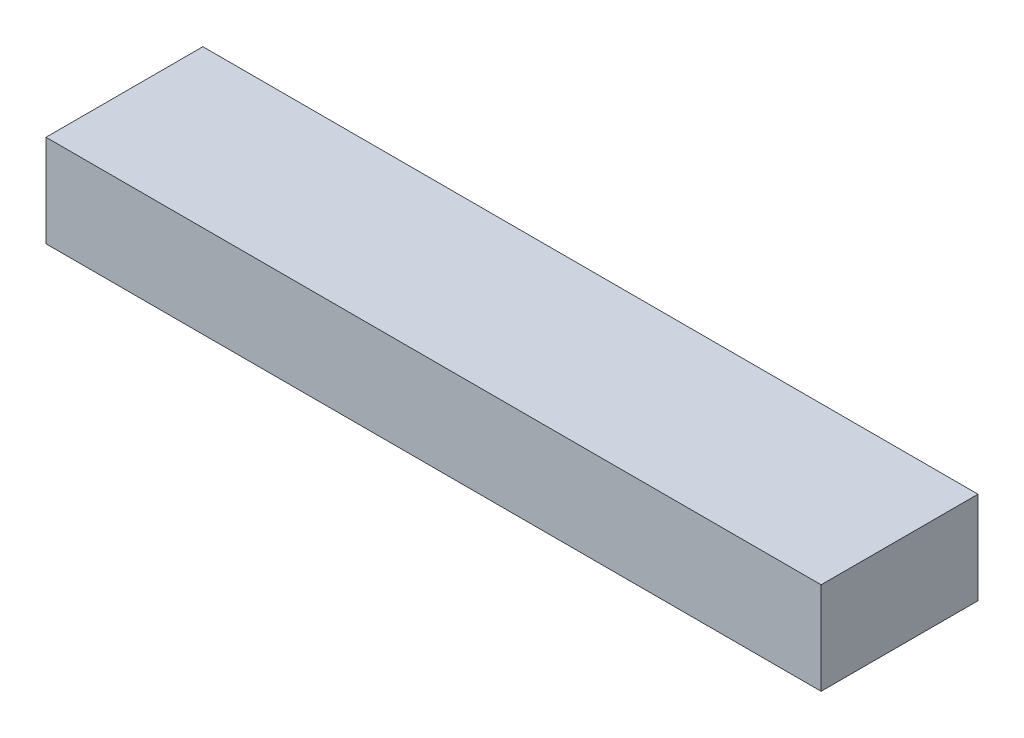
SolidWorks part; units mm, degrees
ref_plane "Front Plane" through (0, 0, 0) normal (0, 0, 1) x (1, 0, 0)
ref_plane "Top Plane" through (0, 0, 0) normal (0, 1, 0) x (1, 0, 0)
ref_plane "Right Plane" through (0, 0, 0) normal (1, 0, 0) x (0, 0, -1)
sketch "Sketch1" plane through (0, 0, 0) normal (0, 1, 0) x (1, 0, 0)
  line L0 (-42, 0) -> (-42, 15)
  line L1 (-42, 15) -> (42, 15)
  line L3 (-42, -2) -> (42, -2)
  line L5 (42, 15) -> (42, 0)
  line L6 (42, 0) -> (42, -2)
  line L7 (-42, -2) -> (-42, 0)
  point P0 (0, 0)
  dimension "D1" = 84
  dimension "D2" = 15
  dimension "D3" = 2
  dimension "D4" = 0
extrude "Boss-Extrude1" add sketch "Sketch1" along normal blind 10
sketch "Sketch2" plane through (0, 0, 0) normal (0, 1, 0) x (1, 0, 0)
  circle A0 centre (0, 0) radius 1
  dimension "D1" = 2
extrude "Cut-Extrude1" cut sketch "Sketch2" along normal blind 0.0001
